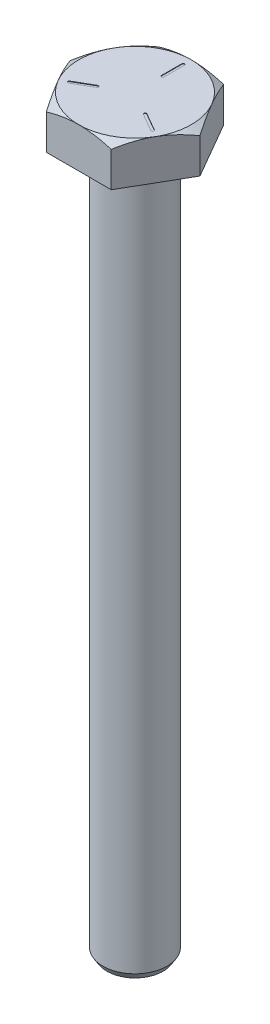
SolidWorks part; units mm, degrees
ref_plane "Front Plane" through (0, 0, 0) normal (0, 0, 1) x (1, 0, 0)
ref_plane "Top Plane" through (0, 0, 0) normal (0, 1, 0) x (1, 0, 0)
ref_plane "Right Plane" through (0, 0, 0) normal (1, 0, 0) x (0, 0, -1)
sketch "Sketch1" plane through (0, 0, 0) normal (0, 1, 0) x (1, 0, 0)
  line L1 (6.4158, 0) -> (3.2079, 5.5562)
  line L2 (3.2079, 5.5562) -> (-3.2079, 5.5562)
  line L3 (-3.2079, 5.5562) -> (-6.4158, 0)
  line L4 (-6.4158, 0) -> (-3.2079, -5.5563)
  line L5 (-3.2079, -5.5563) -> (3.2079, -5.5562)
  line L6 (3.2079, -5.5562) -> (6.4158, 0)
  circle A0 centre (0, 0) radius 5.5562 construction
  dimension "D1" = 11.1125
extrude "Boss-Extrude1" add sketch "Sketch1" along normal blind 3.9624
sketch "Sketch2" plane through (0, 0, 0) normal (0, 0, 1) x (1, 0, 0)
  line L0 (5.5563, 3.9624) -> (6.4158, 3.4544)
  line L2 (6.4158, 3.9624) -> (6.4158, 0) construction
  line L3 (6.4158, 3.4544) -> (6.4158, 3.9624)
  line L4 (6.4158, 3.9624) -> (5.5563, 3.9624)
  line L5 (0, 0) -> (0, 3.9624) construction
  line L6 (-3.2079, 0) -> (3.2079, 0) construction
  line L7 (-3.2079, 3.9624) -> (3.2079, 3.9624) construction
  line L8 (6.4158, 3.9624) -> (6.4158, 0) construction
  line L9 (3.2079, 3.9624) -> (6.4158, 3.9624) construction
  dimension "D1" = 5.5562
  dimension "D2" = 0.508
revolve "Cut-Revolve1" cut sketch "Sketch2" angle 360 about L5
sketch "Sketch3" plane through (0, 3.9624, 0) normal (0, -1, 0) x (-1, 0, 0)
  line L0 (0, 4.7625) -> (0, 2.7305) construction
  line L1 (0.127, 4.7625) -> (0.127, 2.7305)
  line L2 (-0.127, 4.7625) -> (-0.127, 2.7305)
  line L3 (4.1244, -2.3812) -> (2.3647, -1.3652) construction
  line L4 (4.0609, -2.4912) -> (2.3012, -1.4752)
  line L5 (4.1879, -2.2713) -> (2.4282, -1.2553)
  line L6 (-4.1244, -2.3812) -> (-2.3647, -1.3652) construction
  line L7 (-4.1879, -2.2713) -> (-2.4282, -1.2553)
  line L8 (-4.0609, -2.4912) -> (-2.3012, -1.4752)
  arc A0 (0.127, 4.7625) -> (-0.127, 4.7625) centre (0, 4.7625) ccw
  arc A1 (-0.127, 2.7305) -> (0.127, 2.7305) centre (0, 2.7305) ccw
  arc A2 (4.0609, -2.4912) -> (4.1879, -2.2713) centre (4.1244, -2.3812) ccw
  arc A3 (2.4282, -1.2553) -> (2.3012, -1.4752) centre (2.3647, -1.3652) ccw
  arc A4 (-4.1879, -2.2713) -> (-4.0609, -2.4912) centre (-4.1244, -2.3812) ccw
  arc A5 (-2.3012, -1.4752) -> (-2.4282, -1.2553) centre (-2.3647, -1.3652) ccw
  point P3 (0, 3.7465)
  point P12 (3.2446, -1.8732)
  point P19 (-3.2446, -1.8732)
  point P24 (0, 0)
  dimension "D1" = 0.127
  dimension "D2" = 2.032
  dimension "D3" = 4.7625
  dimension "D4" = 3
extrude "Cut-Extrude1" cut sketch "Sketch3" along normal blind 0.0508
sketch "Sketch6" plane through (0, 0, 0) normal (0, 0, 1) x (1, 0, 0)
  line L0 (0, 0) -> (0, 3.302)
  line L1 (0, 3.302) -> (2.7381, 3.302)
  line L3 (3.2079, 3.9624) -> (6.4158, 3.9624) construction
  line L5 (5.4445, 0) -> (5.526, 0.4016)
  line L8 (6.4158, 0) -> (5.4445, 0)
  line L9 (-3.2079, 0) -> (3.2079, 0) construction
  line L10 (0, 3.302) -> (0, 3.9624)
  line L11 (0, 3.9624) -> (5.5563, 3.9624)
  line L12 (5.5562, 3.9624) -> (4.8119, 3.9624) construction
  line L13 (5.5563, 3.9624) -> (6.4158, 3.4544)
  line L14 (6.4158, 3.4544) -> (6.4158, 0)
  line L15 (0, 3.9624) -> (0, 3.302)
  arc A0 (2.8154, 3.2831) -> (5.5127, 0.508) centre (-0.014, -2.1652) cw
  arc A1 (2.7381, 3.302) -> (2.8154, 3.2831) centre (2.7381, 3.1344) cw
  arc A2 (5.526, 0.4016) -> (5.5127, 0.508) centre (5.3617, 0.435) ccw
  point P13 (2.7788, 3.302)
  point P16 (5.5372, 0.4566)
  dimension "D6" = 6.1392
  dimension "D7" = 0.1676
  dimension "D1" = 0.508
  dimension "D2" = 2.7788
  dimension "D3" = 101.48
  dimension "D4" = 5.5372
  dimension "D5" = 3.302
revolve "Cut-Revolve2" [suppressed] cut sketch "Sketch6" angle 360 about L0
sketch "Sketch7" [suppressed] plane through (0, 2.5654, 0) normal (0, 1, 0) x (1, 0, 0)
  line L1 (1.8331, 0) -> (0.9165, 1.5875)
  line L2 (0.9165, 1.5875) -> (-0.9165, 1.5875)
  line L3 (-0.9165, 1.5875) -> (-1.8331, 0)
  line L4 (-1.8331, 0) -> (-0.9165, -1.5875)
  line L5 (-0.9165, -1.5875) -> (0.9165, -1.5875)
  line L6 (0.9165, -1.5875) -> (1.8331, 0)
  circle A0 centre (0, 0) radius 1.5875 construction
  dimension "D1" = 3.9688
extrude "Cut-Extrude2" [suppressed] cut sketch "Sketch7" against normal blind 1.524
sketch "Sketch8" [suppressed] plane through (0, 0, 0) normal (0, 0, 1) x (1, 0, 0)
  line L0 (-1.8331, 2.5654) -> (-1.5283, 2.3876)
  line L1 (-1.5283, 2.3876) -> (-1.5283, 2.5654)
  line L2 (-1.5283, 2.5654) -> (-1.8331, 2.5654)
  line L3 (0, 0) -> (0, -30.4461) construction
  line L4 (-1.5283, 2.3876) -> (0, 2.3876)
  line L5 (0, 2.3876) -> (0, 2.5654)
  line L6 (0, 2.5654) -> (-1.5283, 2.5654)
  dimension "D1" = 0.1778
  dimension "D2" = 0.3048
revolve "Cut-Revolve3" [suppressed] cut sketch "Sketch8" angle 360 about L3
sketch "Sketch9" [suppressed] plane through (0, 3.9624, 0) normal (0, 1, 0) x (-1, 0, 0)
  line L0 (-4.8119, 2.7781) -> (-6.4158, 0) construction
  line L1 (-6.4158, 0) -> (-4.8119, -2.7781) construction
  line L2 (-4.8119, -2.7781) -> (-3.2079, -5.5562) construction
  line L3 (-3.2079, -5.5562) -> (0, -5.5563) construction
  line L4 (3.2079, -5.5562) -> (4.8119, -2.7781) construction
  line L5 (0, -5.5563) -> (3.2079, -5.5562) construction
  line L6 (6.4158, 0) -> (4.8119, 2.7781) construction
  line L7 (4.8119, -2.7781) -> (6.4158, 0) construction
  line L8 (3.2079, 5.5563) -> (0, 5.5563) construction
  line L9 (4.8119, 2.7781) -> (3.2079, 5.5563) construction
  line L10 (0, 5.5563) -> (-3.2079, 5.5562) construction
  line L11 (-3.2079, 5.5562) -> (-4.8119, 2.7781) construction
  line L12 (-4.8119, 2.7781) -> (-6.4158, 0)
  line L13 (-6.4158, 0) -> (-4.8119, -2.7781)
  line L14 (-4.8119, -2.7781) -> (-3.2079, -5.5562)
  line L15 (-3.2079, -5.5562) -> (0, -5.5563)
  line L16 (3.2079, -5.5562) -> (4.8119, -2.7781)
  line L17 (0, -5.5563) -> (3.2079, -5.5562)
  line L18 (6.4158, 0) -> (4.8119, 2.7781)
  line L19 (4.8119, -2.7781) -> (6.4158, 0)
  line L20 (3.2079, 5.5563) -> (0, 5.5563)
  line L21 (4.8119, 2.7781) -> (3.2079, 5.5563)
  line L22 (0, 5.5563) -> (-3.2079, 5.5562)
  line L23 (-3.2079, 5.5562) -> (-4.8119, 2.7781)
  circle A0 centre (0, 0) radius 3.9688
  arc A1 (-4.8119, 2.7781) -> (-4.8119, -2.7781) centre (0, 0) ccw construction
  arc A2 (-4.8119, -2.7781) -> (0, -5.5563) centre (0, 0) ccw construction
  arc A3 (0, -5.5563) -> (4.8119, -2.7781) centre (0, 0) ccw construction
  arc A4 (4.8119, -2.7781) -> (4.8119, 2.7781) centre (0, 0) ccw construction
  arc A5 (4.8119, 2.7781) -> (0, 5.5563) centre (0, 0) ccw construction
  arc A6 (0, 5.5563) -> (-4.8119, 2.7781) centre (0, 0) ccw construction
  arc A7 (-4.8119, 2.7781) -> (-4.8119, -2.7781) centre (0, 0) ccw
  arc A8 (-4.8119, -2.7781) -> (0, -5.5563) centre (0, 0) ccw
  arc A9 (0, -5.5563) -> (4.8119, -2.7781) centre (0, 0) ccw
  arc A10 (4.8119, -2.7781) -> (4.8119, 2.7781) centre (0, 0) ccw
  arc A11 (4.8119, 2.7781) -> (0, 5.5563) centre (0, 0) ccw
  arc A12 (0, 5.5563) -> (-4.8119, 2.7781) centre (0, 0) ccw
  dimension "D1" = 9.525
extrude "Cut-Extrude3" [suppressed] cut sketch "Sketch9" against normal through all
sketch "Sketch11" [suppressed] plane through (0, 3.9624, 0) normal (0, -1, 0) x (-1, 0, 0)
  circle A0 centre (0, 0) radius 3.9688 construction
  circle A1 centre (0, 0) radius 3.9688
extrude "Boss-Extrude3" [suppressed] add sketch "Sketch11" against normal blind 2.3876
sketch "Sketch12" [suppressed] plane through (0, 6.35, 0) normal (0, -1, 0) x (-1, 0, 0)
  line L1 (2.2914, 0) -> (1.1457, 1.9844)
  line L2 (1.1457, 1.9844) -> (-1.1457, 1.9844)
  line L3 (-1.1457, 1.9844) -> (-2.2914, 0)
  line L4 (-2.2914, 0) -> (-1.1457, -1.9844)
  line L5 (-1.1457, -1.9844) -> (1.1457, -1.9844)
  line L6 (1.1457, -1.9844) -> (2.2914, 0)
  circle A0 centre (0, 0) radius 1.9844 construction
  dimension "D1" = 4.7625
extrude "Cut-Extrude4" [suppressed] cut sketch "Sketch12" along normal blind 3.175
fillet "Fillet1" [suppressed] radius 0.3175
sketch "Sketch14" [suppressed] plane through (0, 0, 0) normal (0, 0, 1) x (1, 0, 0)
  line L0 (-2.3454, 5.9531) -> (-3.0328, 6.35)
  line L1 (3.6513, 6.35) -> (-3.6513, 6.35) construction
  line L2 (-3.0328, 6.35) -> (0, 6.35)
  line L3 (0, 6.35) -> (0, 5.9531)
  line L5 (0, 5.9531) -> (-2.3454, 5.9531)
  dimension "D1" = 3.0328
  dimension "D2" = 30
  dimension "D3" = 0.7937
revolve "Cut-Revolve4" [suppressed] cut sketch "Sketch14" angle 360 about L3
sketch "Bolt Length Sketch" plane through (0, 0, 0) normal (0, 0, 1) x (1, 0, 0)
  line L0 (0, 0) -> (0, -69.85)
  line L1 (0, -69.85) -> (2.7781, -69.85)
  line L2 (2.7781, -69.85) -> (3.175, -69.215)
  line L3 (3.175, -69.215) -> (3.175, 0)
  line L6 (0, 0) -> (3.175, 0)
  dimension "D1" = 3.175
  dimension "D2" = 0.635
  dimension "D3" = 0.3969
  dimension "D4" = 69.85
revolve "Bolt Length" add sketch "Bolt Length Sketch" angle 360 about L0
